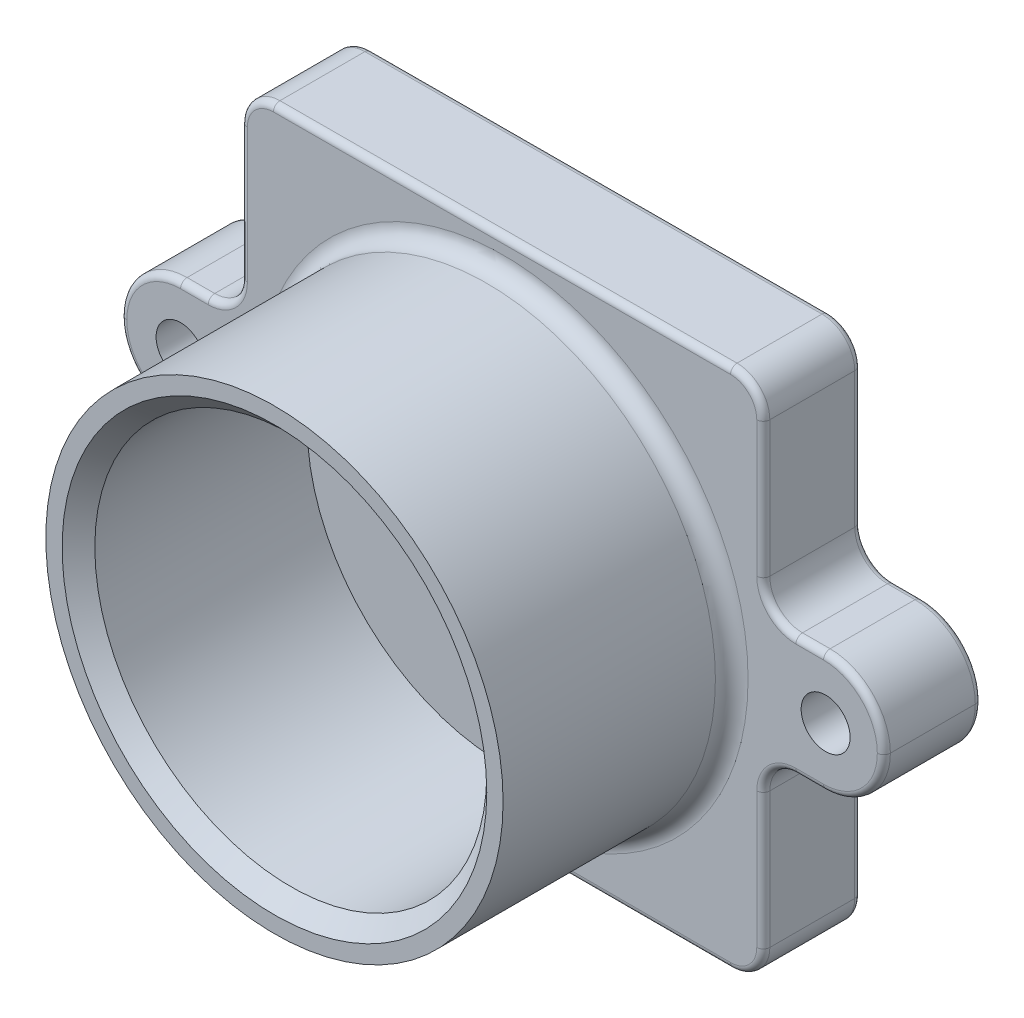
SolidWorks part; units mm, degrees
ref_plane "Front Plane" through (0, 0, 0) normal (0, 0, 1) x (1, 0, 0)
ref_plane "Top Plane" through (0, 0, 0) normal (0, 1, 0) x (1, 0, 0)
ref_plane "Right Plane" through (0, 0, 0) normal (1, 0, 0) x (0, 0, -1)
sketch "Sketch1" plane through (0, 0, 0) normal (0, 0, 1) x (1, 0, 0)
  line L0 (-203.9221, 202.4782) -> (202.3289, 203.6035)
  line L1 (-203.9221, 202.4782) -> (-203.9221, 47.3531)
  line L2 (-203.9221, 47.3531) -> (-250.7973, 47.3531)
  line L3 (-250.7973, -46.3972) -> (-203.9221, -46.3972)
  line L4 (-203.9221, -46.3972) -> (-203.9221, -202.6475)
  line L5 (-203.9221, -202.6475) -> (202.3289, -202.6475)
  line L6 (202.3289, -202.6475) -> (202.3289, -46.3972)
  line L7 (202.3289, -46.3972) -> (249.204, -46.3972)
  line L8 (249.204, 47.3531) -> (202.3289, 47.3531)
  line L9 (202.3289, 47.3531) -> (202.3289, 203.6035)
  arc A0 (-250.7973, 47.3531) -> (-297.6724, 0.478) centre (-250.7973, 0.478) ccw
  arc A1 (-297.6724, 0.478) -> (-250.7973, -46.3972) centre (-250.7973, 0.4779) ccw
  arc A2 (249.204, -46.3972) -> (296.0792, 0.478) centre (249.204, 0.4779) ccw
  arc A3 (296.0792, 0.478) -> (249.204, 47.3531) centre (249.204, 0.478) ccw
extrude "Boss-Extrude1" add sketch "Sketch1" along normal blind 254
sketch "Sketch2" plane through (0, 0, 254) normal (0, 0, 1) x (1, 0, 0)
  line L0 (-297.6724, 0.478) -> (296.0792, 0.4779) construction
  line L1 (-0.7966, 203.0408) -> (-0.7966, -202.6475) construction
  line L2 (202.3289, 203.6035) -> (-203.9221, 202.4782) construction
  line L3 (-203.9221, -202.6475) -> (202.3289, -202.6475) construction
  arc A0 (-250.7973, 47.3531) -> (-297.6724, 0.478) centre (-250.7973, 0.478) ccw construction
  arc A1 (249.204, -46.3972) -> (296.0792, 0.478) centre (249.204, 0.4779) ccw construction
  circle A2 centre (0, 0) radius 177.8
  dimension "D1" = 355.6
extrude "Cut-Extrude1" cut sketch "Sketch2" against normal blind 177.8 flip side to cut
sketch "Sketch3" plane through (0, 0, 254) normal (0, 0, 1) x (1, 0, 0)
  circle A0 centre (0, 0) radius 152.4
  dimension "D1" = 304.8
extrude "Cut-Extrude2" cut sketch "Sketch3" against normal up to surface (177.8 mm away) up to face at (177.8, 0, 76.2)
sketch "Sketch4" plane through (0, 0, 76.2) normal (0, 0, 1) x (1, 0, 0)
  line L0 (0, 76.2713) -> (0, -65.9494) construction
  circle A0 centre (-250.7973, 0.478) radius 19.05
  circle A1 centre (250.7973, 0.478) radius 19.05
  dimension "D1" = 38.1
extrude "Cut-Extrude3" cut sketch "Sketch4" against normal through all
fillet "Fillet1" radius 25.4 8 edges at (-203.9221, -46.3972, 38.1) (202.3289, -46.3972, 38.1) (202.3289, 47.3531, 38.1) (-203.9221, 47.3531, 38.1) (-203.9221, -202.6475, 38.1) (202.3289, -202.6475, 38.1) (202.3289, 203.6035, 38.1) (-203.9221, 202.4782, 38.1)
fillet "Fillet2" radius 12.7 1 edges at (177.8, 0, 76.2)
chamfer "Chamfer1" distance 12.7 angle 45 1 edges at (152.4, 0, 254)
fillet "Fillet3" radius 5.08 44 edges at (209.7683, 54.7926, 0) (238.4664, 47.3531, 0) (282.3498, 33.6237, 0) (282.3498, -32.6678, 0) (238.4664, -46.3972, 0) (209.7683, -53.8367, 0) (202.3289, -124.5223, 0) (194.8894, -195.208, 0) (-0.7966, -202.6475, 0) (-196.4826, -195.208, 0) (-203.9221, -124.5223, 0) (-211.3616, -53.8367, 0) (-240.0597, -46.3972, 0) (-283.943, -32.6678, 0) (-283.943, 33.6237, 0) (-240.0597, 47.3531, 0) (-211.3616, 54.7926, 0) (-203.9221, 124.9508, 0) (-196.5075, 195.0841, 0) (-0.867, 203.0406, 0) (194.8645, 196.1184, 0) (209.7683, 54.7926, 76.2) (238.4664, 47.3531, 76.2) (282.3498, 33.6237, 76.2) (282.3498, -32.6678, 76.2) (238.4664, -46.3972, 76.2) (209.7683, -53.8367, 76.2) (202.3289, -124.5223, 76.2) (194.8894, -195.208, 76.2) (-0.7966, -202.6475, 76.2) (-196.4826, -195.208, 76.2) (-203.9221, -124.5223, 76.2) (-211.3616, -53.8367, 76.2) (-240.0597, -46.3972, 76.2) (-283.943, -32.6678, 76.2) (-283.943, 33.6237, 76.2) (-240.0597, 47.3531, 76.2) (-211.3616, 54.7926, 76.2) (-203.9221, 124.9508, 76.2) (-196.5075, 195.0841, 76.2) (-0.867, 203.0406, 76.2) (194.8645, 196.1184, 76.2) (202.3289, 125.4431, 0) (202.3289, 125.4431, 76.2)
